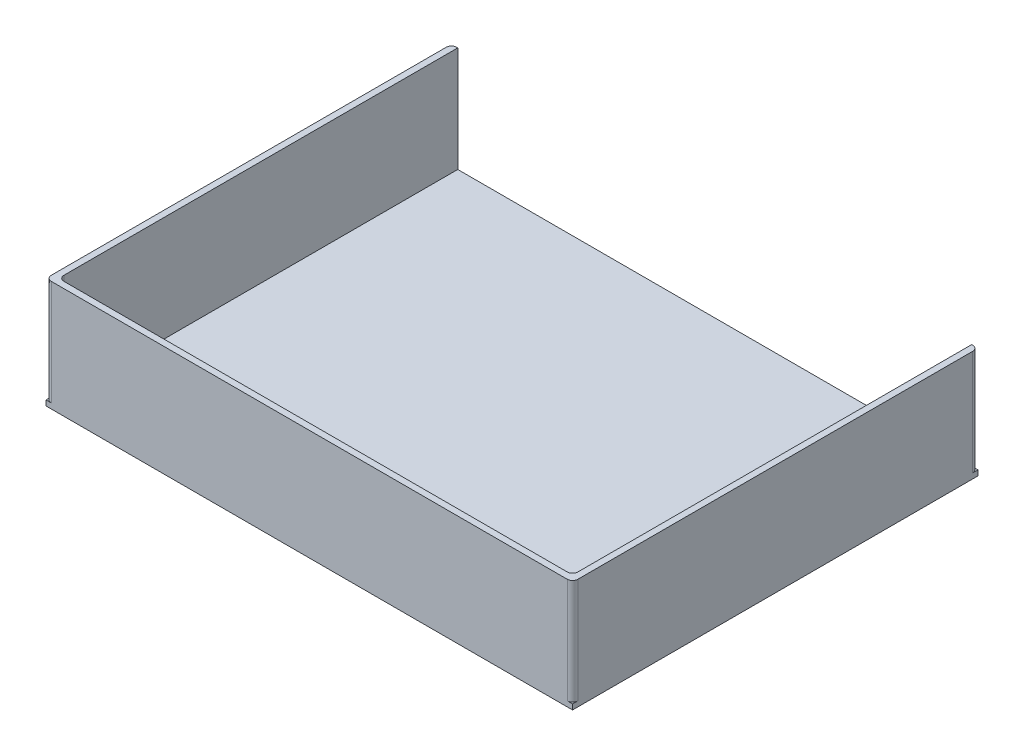
SolidWorks part; units mm, degrees
ref_plane "Alzado" through (0, 0, 0) normal (0, 0, 1) x (1, 0, 0)
ref_plane "Planta" through (0, 0, 0) normal (0, 1, 0) x (1, 0, 0)
ref_plane "Vista lateral" through (0, 0, 0) normal (1, 0, 0) x (0, 0, -1)
sketch "Croquis1" plane through (0, 0, 0) normal (0, 1, 0) x (1, 0, 0)
  line L1 (-250, -192.5) -> (250, -192.5)
  line L2 (-250, -192.5) -> (-250, 192.5)
  line L3 (-250, 192.5) -> (250, 192.5)
  line L4 (250, -192.5) -> (250, 192.5)
  line L5 (-250, -192.5) -> (250, 192.5) construction
  line L6 (-250, 192.5) -> (250, -192.5) construction
  point P0 (0, 0)
  dimension "D1" = 500
  dimension "D2" = 385
extrude "Saliente-Extruir1" add sketch "Croquis1" along normal blind 5
sketch "Croquis2" plane through (0, 5, 0) normal (0, 1, 0) x (1, 0, 0)
  line L0 (-244, 186.5) -> (-244, -181.5)
  line L1 (-239, -186.5) -> (239, -186.5)
  line L2 (244, -181.5) -> (244, 186.5)
  line L4 (250, -192.5) -> (250, 192.5)
  line L5 (250, 192.5) -> (-250, 192.5)
  line L6 (-250, 192.5) -> (-250, -192.5)
  line L7 (-250, -192.5) -> (250, -192.5)
  line L8 (250, -187.5) -> (250, 187.5)
  line L9 (245, 192.5) -> (244, 192.5)
  line L10 (-250, 187.5) -> (-250, -187.5)
  line L11 (-245, -192.5) -> (245, -192.5)
  line L12 (-244, 186.5) -> (-244, 192.5)
  line L13 (244, 186.5) -> (244, 192.5)
  line L14 (-244, 192.5) -> (-245, 192.5)
  line L15 (244, 186.5) -> (-244, 186.5) construction
  line L16 (250, 192.5) -> (-250, 192.5) construction
  line L17 (-250, 192.5) -> (-250, -192.5) construction
  line L18 (250, -192.5) -> (250, 192.5) construction
  line L19 (-250, -192.5) -> (250, -192.5) construction
  line L20 (-244, -186.5) -> (244, -186.5) construction
  line L21 (244, -186.5) -> (244, 186.5) construction
  line L22 (-244, 186.5) -> (-244, -186.5) construction
  arc A0 (-250, 187.5) -> (-245, 192.5) centre (-245, 187.5) cw
  arc A1 (250, 187.5) -> (245, 192.5) centre (245, 187.5) ccw
  arc A2 (250, -187.5) -> (245, -192.5) centre (245, -187.5) cw
  arc A3 (239, -186.5) -> (244, -181.5) centre (239, -181.5) ccw
  arc A4 (-244, -181.5) -> (-239, -186.5) centre (-239, -181.5) ccw
  arc A5 (-245, -192.5) -> (-250, -187.5) centre (-245, -187.5) cw
  dimension "D3" = 5
  dimension "D4" = 5
  dimension "D1" = 0
  dimension "D2" = 6
extrude "Saliente-Extruir2" add sketch "Croquis2" along normal blind 100
